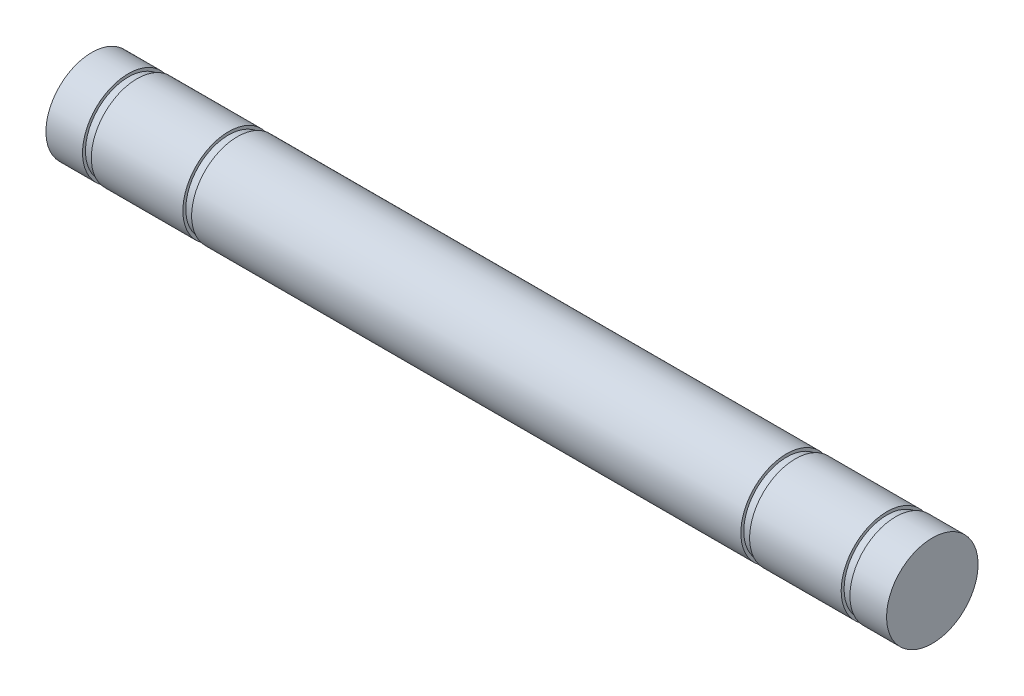
SolidWorks part; units mm, degrees
material "A-Glass Fiber"
ref_plane "Front" through (0, 0, 0) normal (0, 0, 1) x (1, 0, 0)
ref_plane "Top" through (0, 0, 0) normal (0, 1, 0) x (1, 0, 0)
ref_plane "Right" through (0, 0, 0) normal (1, 0, 0) x (0, 0, -1)
sketch "Sketch1" plane through (0, 0, 0) normal (0, 0, 1) x (1, 0, 0)
  line L0 (-25.4, 0) -> (25.4, 0) construction
  line L1 (25.4, 1.5875) -> (25.4, -1.5875) construction
  line L2 (-25.4, 1.5875) -> (-25.4, -1.5875) construction
  dimension "Length" = 50.8
  dimension "Diameter" = 3.175
sketch "Sketch2" plane through (0, 0, 0) normal (1, 0, 0) x (0, 0, -1)
  circle A0 centre (0, 0) radius 1.5875
extrude "Extrude1" add sketch "Sketch2" against normal up to vertex (25.4 mm away) and the other way up to vertex (25.4 mm away) up to point (-25.4, 1.5875, 0) other way up to point (25.4, 1.5875, 0)
chamfer "Chamfer1" distance 0.3175 angle 45 2 edges at (25.4, 0, -1.5875) (-25.4, 0, -1.5875)
ref_plane "Plane1" through (19.05, 0, 0) normal (1, 0, 0) x (0, 0, -1)
ref_plane "Plane2" through (0, 0, 0) normal (1, 0, 0) x (0, 0, -1)
sketch "Sketch3" plane through (19.05, 0, 0) normal (1, 0, 0) x (0, 0, -1)
  circle A0 centre (0, 0) radius 1.4859
  dimension "D1" = 2.9718
extrude "Cut-Extrude1" cut sketch "Sketch3" along normal blind 0.3048 flip side to cut
sketch "Sketch4" plane through (0, 0, 0) normal (1, 0, 0) x (0, 0, -1)
  circle A0 centre (0, 0) radius 1.4859
  dimension "D1" = 2.9718
extrude "Cut-Extrude2" cut sketch "Sketch4" against normal blind 0.3048 flip side to cut
sketch "Sketch6" plane through (19.3548, 0, 0) normal (-1, 0, 0) x (0, 0, 1)
  circle A0 centre (0, 0) radius 1.4859
  dimension "D1" = 2.9718
extrude "Cut-Extrude4" cut sketch "Sketch6" against normal blind 0.3048 from offset 3.175 flip side to cut offset against normal yes
sketch "Sketch8" plane through (-0.3048, 0, 0) normal (1, 0, 0) x (0, 0, -1)
  circle A0 centre (0, 0) radius 1.4859
  dimension "D1" = 2.9718
extrude "Cut-Extrude5" cut sketch "Sketch8" against normal blind 0.3048 from offset 3.175 flip side to cut offset against normal yes
sketch "Sketch5" plane through (0, 0, 0) normal (0, 0, 1) x (1, 0, 0)
  line L0 (25.4, -1.27) -> (25.4, 1.27) construction
  line L1 (-25.4, 3.175) -> (-5.0546, 3.175)
  line L2 (-25.4, 3.175) -> (-25.4, -3.175)
  line L3 (-25.4, -3.175) -> (-5.0546, -3.175)
  line L4 (-5.0546, 3.175) -> (-5.0546, -3.175)
  line L5 (24.1046, 3.175) -> (25.4, 3.175)
  line L6 (24.1046, 3.175) -> (24.1046, -3.175)
  line L7 (24.1046, -3.175) -> (25.4, -3.175)
  line L8 (25.4, 3.175) -> (25.4, -3.175)
  line L12 (-25.4, 1.27) -> (-25.4, -1.27) construction
  line L14 (-3.7846, -1.5875) -> (-3.7846, 1.5875) construction
  line L16 (22.8346, 1.5875) -> (22.8346, -1.5875) construction
  line L17 (-25.4, 0) -> (25.4, 0) construction
  dimension "D1" = 1.27
  dimension "D2" = 1.27
  dimension "D3" = 6.35
extrude "Cut-Extrude3" cut sketch "Sketch5" against normal through all both and the other way through all
equation "\"D1@Chamfer1\" = \"Diameter@Sketch1\"*.1"
